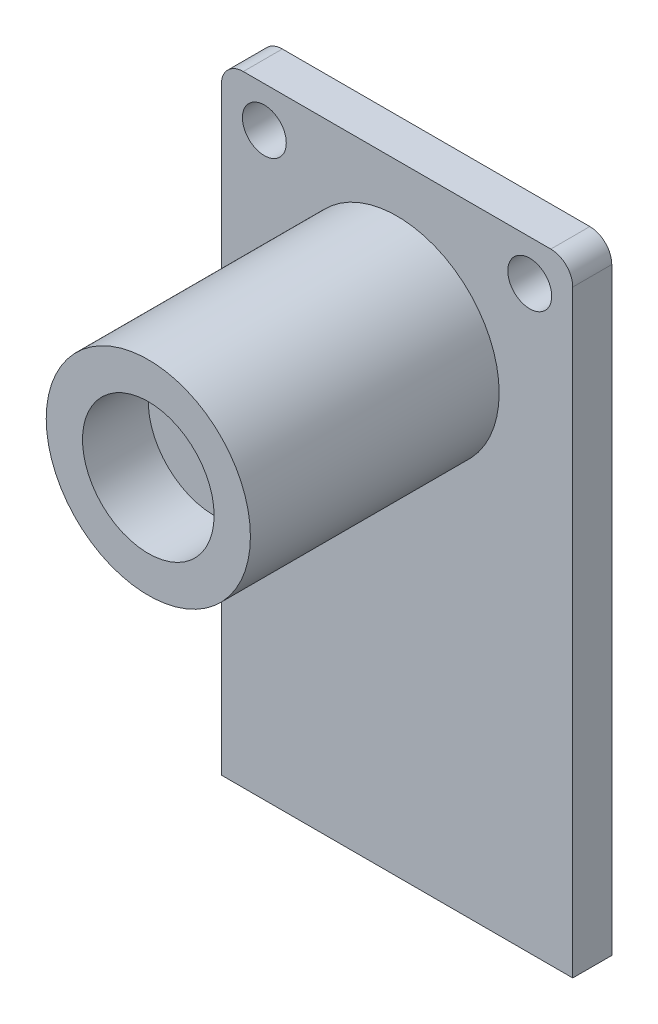
SolidWorks part; units mm, degrees
ref_plane "Front Plane" through (0, 0, 0) normal (0, 0, 1) x (1, 0, 0)
ref_plane "Top Plane" through (0, 0, 0) normal (0, 1, 0) x (1, 0, 0)
ref_plane "Right Plane" through (0, 0, 0) normal (1, 0, 0) x (0, 0, -1)
sketch "Sketch1" plane through (0, 0, 0) normal (0, 0, 1) x (1, 0, 0)
  line L1 (8.01, -14.14) -> (-8.01, -14.14)
  line L2 (8.01, -14.14) -> (8.01, 13.14)
  line L3 (7.01, 14.14) -> (-7.01, 14.14)
  line L4 (-8.01, -14.14) -> (-8.01, 13.14)
  arc A0 (8.01, 13.14) -> (7.01, 14.14) centre (7.01, 13.14) ccw
  arc A1 (-8.01, 13.14) -> (-7.01, 14.14) centre (-7.01, 13.14) cw
  point P0 (0, 0)
  dimension "D1" = 1
  dimension "D2" = 16.02
  dimension "D3" = 28.28
extrude "Boss-Extrude1" add sketch "Sketch1" along normal blind 1.78
sketch "Sketch2" plane through (0, 0, 1.78) normal (0, 0, 1) x (1, 0, 0)
  line L0 (7.01, 14.14) -> (-7.01, 14.14) construction
  circle A0 centre (0, 7.285) radius 4.655
  dimension "D1" = 6.855
extrude "Boss-Extrude2" add sketch "Sketch2" along normal blind 11.34
sketch "Sketch3" plane through (0, 0, 13.12) normal (0, 0, 1) x (1, 0, 0)
  circle A0 centre (0, 7.285) radius 3
extrude "Cut-Extrude1" cut sketch "Sketch3" against normal blind 3
sketch "Sketch4" plane through (0, 0, 1.78) normal (0, 0, 1) x (1, 0, 0)
  circle A1 centre (6.05, 12.2999) radius 1
  circle A2 centre (-6.05, 12.2999) radius 1
extrude "Cut-Extrude2" cut sketch "Sketch4" against normal blind 3
